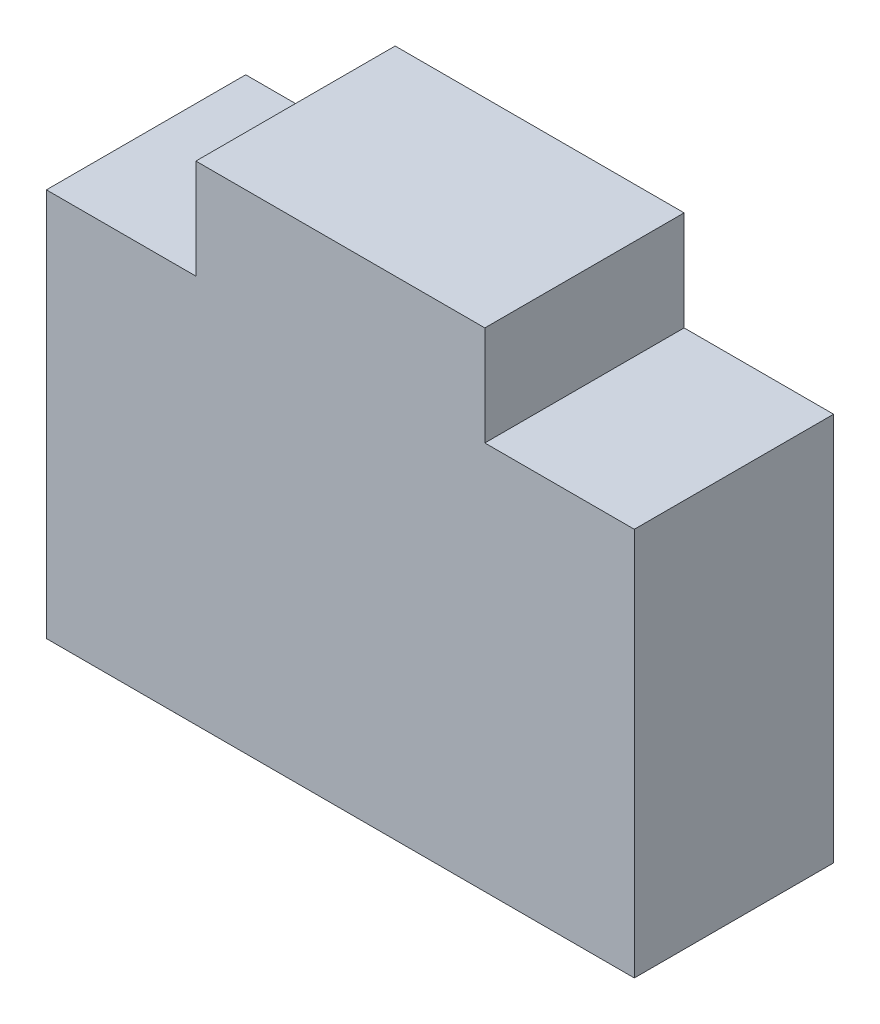
SolidWorks part; units mm, degrees
ref_plane "Front Plane" through (0, 0, 0) normal (0, 0, 1) x (1, 0, 0)
ref_plane "Top Plane" through (0, 0, 0) normal (0, 1, 0) x (1, 0, 0)
ref_plane "Right Plane" through (0, 0, 0) normal (1, 0, 0) x (0, 0, -1)
sketch "Sketch1" plane through (0, 0, 0) normal (0, 0, 1) x (1, 0, 0)
  line L0 (-1.45, 0) -> (1.45, 0)
  line L1 (1.45, 0) -> (1.45, -1)
  line L2 (1.45, -1) -> (2.95, -1)
  line L3 (2.95, -1) -> (2.95, -4.9)
  line L4 (2.95, -4.9) -> (-2.95, -4.9)
  line L5 (0, -1000) -> (0, 49000) construction
  line L6 (-2.95, -1) -> (-2.95, -4.9)
  line L7 (-1.45, -1) -> (-2.95, -1)
  line L8 (-1.45, 0) -> (-1.45, -1)
  point P10 (0, -4.9)
  point P13 (0, 0)
  dimension "D1" = 1.45
  dimension "D2" = 1
  dimension "D3" = 1.5
  dimension "D4" = 3.9
extrude "Boss-Extrude1" add sketch "Sketch1" along normal blind 2
